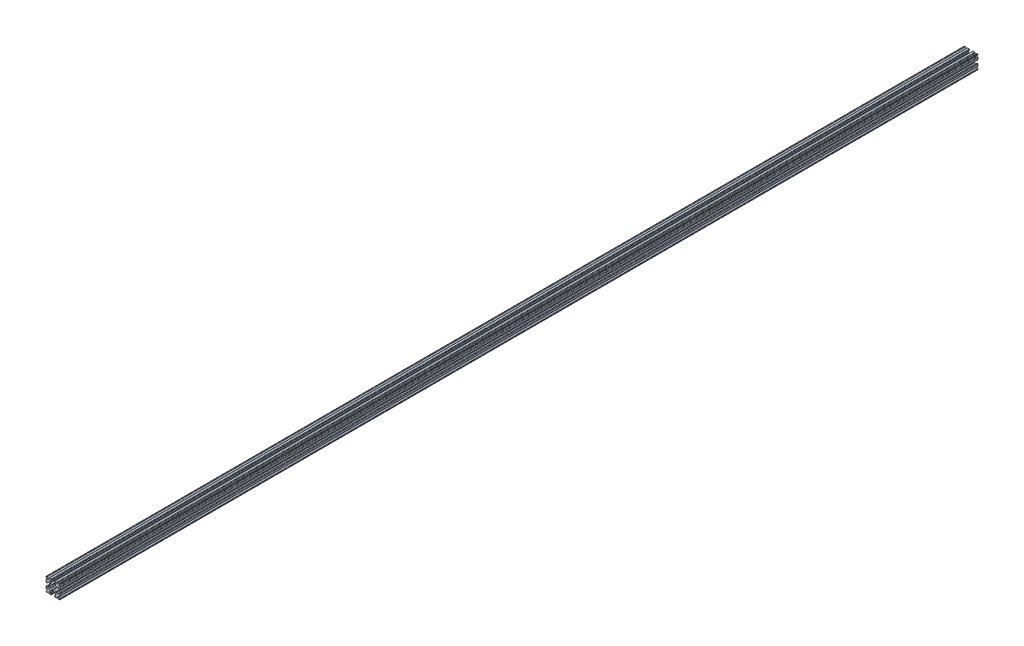
SolidWorks part; units mm, degrees
material "6063-T5"
ref_plane "Plano frontal" through (0, 0, 0) normal (0, 0, 1) x (1, 0, 0)
ref_plane "Plano superior" through (0, 0, 0) normal (0, 1, 0) x (1, 0, 0)
ref_plane "Plano direito" through (0, 0, 0) normal (1, 0, 0) x (0, 0, -1)
sketch "Model" plane through (0, 0, 0) normal (0, 0, 1) x (1, 0, 0)
  line L0 (53.34, -190.5) -> (99.06, -190.5)
  line L1 (111.76, -177.8) -> (111.76, -169.3613)
  line L2 (133.4403, -160.381) -> (159.8395, -186.7803)
  line L3 (168.8197, -190.5) -> (184.15, -190.5)
  line L4 (190.5, -184.15) -> (190.5, -168.8197)
  line L5 (186.7803, -159.8395) -> (160.381, -133.4403)
  line L6 (169.3613, -111.76) -> (177.8, -111.76)
  line L7 (190.5, -99.06) -> (190.5, -53.34)
  line L8 (177.8, -40.64) -> (167.64, -40.64)
  line L9 (154.94, -53.34) -> (154.94, -68.58)
  line L10 (149.86, -73.66) -> (96.5285, -73.66)
  line L11 (84.136, -63.7376) -> (80.2326, -46.3223)
  line L12 (80.2326, -46.3223) -> (33.4507, -19.3128)
  line L13 (33.4507, 19.3128) -> (80.2326, 46.3223)
  line L14 (80.2326, 46.3223) -> (84.136, 63.7376)
  line L15 (96.5285, 73.66) -> (149.86, 73.66)
  line L16 (154.94, 68.58) -> (154.94, 53.34)
  line L17 (167.64, 40.64) -> (177.8, 40.64)
  line L18 (190.5, 53.34) -> (190.5, 99.06)
  line L19 (177.8, 111.76) -> (169.3613, 111.76)
  line L20 (160.381, 133.4403) -> (186.7803, 159.8395)
  line L21 (190.5, 168.8197) -> (190.5, 184.15)
  line L22 (184.15, 190.5) -> (168.8197, 190.5)
  line L23 (159.8395, 186.7803) -> (133.4403, 160.381)
  line L24 (111.76, 169.3613) -> (111.76, 177.8)
  line L25 (99.06, 190.5) -> (53.34, 190.5)
  line L26 (40.64, 177.8) -> (40.64, 167.64)
  line L27 (53.34, 154.94) -> (68.58, 154.94)
  line L28 (73.66, 149.86) -> (73.66, 96.5285)
  line L29 (63.7376, 84.136) -> (24.9366, 75.4392)
  line L30 (20.9677, 70.4822) -> (20.9677, 64.6954)
  line L31 (15.8877, 59.6154) -> (-15.8877, 59.6154)
  line L32 (-20.9677, 64.6954) -> (-20.9677, 70.4822)
  line L33 (-24.9366, 75.4392) -> (-63.7376, 84.136)
  line L34 (-73.66, 96.5285) -> (-73.66, 149.86)
  line L35 (-68.58, 154.94) -> (-53.34, 154.94)
  line L36 (-40.64, 167.64) -> (-40.64, 177.8)
  line L37 (-53.34, 190.5) -> (-99.06, 190.5)
  line L38 (-111.76, 177.8) -> (-111.76, 169.3613)
  line L39 (-133.4403, 160.381) -> (-159.8395, 186.7803)
  line L40 (-168.8197, 190.5) -> (-184.15, 190.5)
  line L41 (-190.5, 184.15) -> (-190.5, 168.8197)
  line L42 (-186.7803, 159.8395) -> (-160.381, 133.4403)
  line L43 (-169.3613, 111.76) -> (-177.8, 111.76)
  line L44 (-190.5, 99.06) -> (-190.5, 53.34)
  line L45 (-177.8, 40.64) -> (-167.64, 40.64)
  line L46 (-154.94, 53.34) -> (-154.94, 68.58)
  line L47 (-149.86, 73.66) -> (-96.5285, 73.66)
  line L48 (-84.136, 63.7376) -> (-75.4392, 24.9366)
  line L49 (-70.4822, 20.9677) -> (-64.6954, 20.9677)
  line L50 (-59.6154, 15.8877) -> (-59.6154, -15.8877)
  line L51 (-64.6954, -20.9677) -> (-70.4822, -20.9677)
  line L52 (-75.4392, -24.9366) -> (-84.136, -63.7376)
  line L53 (-96.5285, -73.66) -> (-149.86, -73.66)
  line L54 (-154.94, -68.58) -> (-154.94, -53.34)
  line L55 (-167.64, -40.64) -> (-177.8, -40.64)
  line L56 (-190.5, -53.34) -> (-190.5, -99.06)
  line L57 (-177.8, -111.76) -> (-169.3613, -111.76)
  line L58 (-160.381, -133.4403) -> (-186.7803, -159.8395)
  line L59 (-190.5, -168.8197) -> (-190.5, -184.15)
  line L60 (-184.15, -190.5) -> (-168.8197, -190.5)
  line L61 (-159.8395, -186.7803) -> (-133.4403, -160.381)
  line L62 (-111.76, -169.3613) -> (-111.76, -177.8)
  line L63 (-99.06, -190.5) -> (-53.34, -190.5)
  line L64 (-40.64, -177.8) -> (-40.64, -167.64)
  line L65 (-53.34, -154.94) -> (-68.58, -154.94)
  line L66 (-73.66, -149.86) -> (-73.66, -96.5285)
  line L67 (-63.7376, -84.136) -> (-24.9366, -75.4392)
  line L68 (-20.9677, -70.4822) -> (-20.9677, -64.6954)
  line L69 (-15.8877, -59.6154) -> (15.8877, -59.6154)
  line L70 (20.9677, -64.6954) -> (20.9677, -70.4822)
  line L71 (24.9366, -75.4392) -> (63.7376, -84.136)
  line L72 (73.66, -96.5285) -> (73.66, -149.86)
  line L73 (68.58, -154.94) -> (53.34, -154.94)
  line L74 (40.64, -167.64) -> (40.64, -177.8)
  arc A0 (99.06, -190.5) -> (111.76, -177.8) centre (99.06, -177.8) ccw
  arc A1 (133.4403, -160.381) -> (111.76, -169.3613) centre (124.46, -169.3613) ccw
  arc A2 (159.8395, -186.7803) -> (168.8197, -190.5) centre (168.8197, -177.8) ccw
  arc A3 (184.15, -190.5) -> (190.5, -184.15) centre (184.15, -184.15) ccw
  arc A4 (190.5, -168.8197) -> (186.7803, -159.8395) centre (177.8, -168.8197) ccw
  arc A5 (169.3613, -111.76) -> (160.381, -133.4403) centre (169.3613, -124.46) ccw
  arc A6 (177.8, -111.76) -> (190.5, -99.06) centre (177.8, -99.06) ccw
  arc A7 (190.5, -53.34) -> (177.8, -40.64) centre (177.8, -53.34) ccw
  arc A8 (167.64, -40.64) -> (154.94, -53.34) centre (167.64, -53.34) ccw
  arc A9 (149.86, -73.66) -> (154.94, -68.58) centre (149.86, -68.58) ccw
  arc A10 (84.136, -63.7376) -> (96.5285, -73.66) centre (96.5285, -60.96) ccw
  arc A11 (33.4507, -19.3128) -> (23.9038, -20.8967) centre (29.6407, -25.9119) ccw
  arc A12 (23.9038, 20.8967) -> (23.9038, -20.8967) centre (0, 0) ccw
  arc A13 (23.9038, 20.8967) -> (33.4507, 19.3128) centre (29.6407, 25.9119) ccw
  arc A14 (96.5285, 73.66) -> (84.136, 63.7376) centre (96.5285, 60.96) ccw
  arc A15 (154.94, 68.58) -> (149.86, 73.66) centre (149.86, 68.58) ccw
  arc A16 (154.94, 53.34) -> (167.64, 40.64) centre (167.64, 53.34) ccw
  arc A17 (177.8, 40.64) -> (190.5, 53.34) centre (177.8, 53.34) ccw
  arc A18 (190.5, 99.06) -> (177.8, 111.76) centre (177.8, 99.06) ccw
  arc A19 (160.381, 133.4403) -> (169.3613, 111.76) centre (169.3613, 124.46) ccw
  arc A20 (186.7803, 159.8395) -> (190.5, 168.8197) centre (177.8, 168.8197) ccw
  arc A21 (190.5, 184.15) -> (184.15, 190.5) centre (184.15, 184.15) ccw
  arc A22 (168.8197, 190.5) -> (159.8395, 186.7803) centre (168.8197, 177.8) ccw
  arc A23 (111.76, 169.3613) -> (133.4403, 160.381) centre (124.46, 169.3613) ccw
  arc A24 (111.76, 177.8) -> (99.06, 190.5) centre (99.06, 177.8) ccw
  arc A25 (53.34, 190.5) -> (40.64, 177.8) centre (53.34, 177.8) ccw
  arc A26 (40.64, 167.64) -> (53.34, 154.94) centre (53.34, 167.64) ccw
  arc A27 (73.66, 149.86) -> (68.58, 154.94) centre (68.58, 149.86) ccw
  arc A28 (63.7376, 84.136) -> (73.66, 96.5285) centre (60.96, 96.5285) ccw
  arc A29 (24.9366, 75.4392) -> (20.9677, 70.4822) centre (26.0477, 70.4822) ccw
  arc A30 (15.8877, 59.6154) -> (20.9677, 64.6954) centre (15.8877, 64.6954) ccw
  arc A31 (-20.9677, 64.6954) -> (-15.8877, 59.6154) centre (-15.8877, 64.6954) ccw
  arc A32 (-20.9677, 70.4822) -> (-24.9366, 75.4392) centre (-26.0477, 70.4822) ccw
  arc A33 (-73.66, 96.5285) -> (-63.7376, 84.136) centre (-60.96, 96.5285) ccw
  arc A34 (-68.58, 154.94) -> (-73.66, 149.86) centre (-68.58, 149.86) ccw
  arc A35 (-53.34, 154.94) -> (-40.64, 167.64) centre (-53.34, 167.64) ccw
  arc A36 (-40.64, 177.8) -> (-53.34, 190.5) centre (-53.34, 177.8) ccw
  arc A37 (-99.06, 190.5) -> (-111.76, 177.8) centre (-99.06, 177.8) ccw
  arc A38 (-133.4403, 160.381) -> (-111.76, 169.3613) centre (-124.46, 169.3613) ccw
  arc A39 (-159.8395, 186.7803) -> (-168.8197, 190.5) centre (-168.8197, 177.8) ccw
  arc A40 (-184.15, 190.5) -> (-190.5, 184.15) centre (-184.15, 184.15) ccw
  arc A41 (-190.5, 168.8197) -> (-186.7803, 159.8395) centre (-177.8, 168.8197) ccw
  arc A42 (-169.3613, 111.76) -> (-160.381, 133.4403) centre (-169.3613, 124.46) ccw
  arc A43 (-177.8, 111.76) -> (-190.5, 99.06) centre (-177.8, 99.06) ccw
  arc A44 (-190.5, 53.34) -> (-177.8, 40.64) centre (-177.8, 53.34) ccw
  arc A45 (-167.64, 40.64) -> (-154.94, 53.34) centre (-167.64, 53.34) ccw
  arc A46 (-149.86, 73.66) -> (-154.94, 68.58) centre (-149.86, 68.58) ccw
  arc A47 (-84.136, 63.7376) -> (-96.5285, 73.66) centre (-96.5285, 60.96) ccw
  arc A48 (-75.4392, 24.9366) -> (-70.4822, 20.9677) centre (-70.4822, 26.0477) ccw
  arc A49 (-59.6154, 15.8877) -> (-64.6954, 20.9677) centre (-64.6954, 15.8877) ccw
  arc A50 (-64.6954, -20.9677) -> (-59.6154, -15.8877) centre (-64.6954, -15.8877) ccw
  arc A51 (-70.4822, -20.9677) -> (-75.4392, -24.9366) centre (-70.4822, -26.0477) ccw
  arc A52 (-96.5285, -73.66) -> (-84.136, -63.7376) centre (-96.5285, -60.96) ccw
  arc A53 (-154.94, -68.58) -> (-149.86, -73.66) centre (-149.86, -68.58) ccw
  arc A54 (-154.94, -53.34) -> (-167.64, -40.64) centre (-167.64, -53.34) ccw
  arc A55 (-177.8, -40.64) -> (-190.5, -53.34) centre (-177.8, -53.34) ccw
  arc A56 (-190.5, -99.06) -> (-177.8, -111.76) centre (-177.8, -99.06) ccw
  arc A57 (-160.381, -133.4403) -> (-169.3613, -111.76) centre (-169.3613, -124.46) ccw
  arc A58 (-186.7803, -159.8395) -> (-190.5, -168.8197) centre (-177.8, -168.8197) ccw
  arc A59 (-190.5, -184.15) -> (-184.15, -190.5) centre (-184.15, -184.15) ccw
  arc A60 (-168.8197, -190.5) -> (-159.8395, -186.7803) centre (-168.8197, -177.8) ccw
  arc A61 (-111.76, -169.3613) -> (-133.4403, -160.381) centre (-124.46, -169.3613) ccw
  arc A62 (-111.76, -177.8) -> (-99.06, -190.5) centre (-99.06, -177.8) ccw
  arc A63 (-53.34, -190.5) -> (-40.64, -177.8) centre (-53.34, -177.8) ccw
  arc A64 (-40.64, -167.64) -> (-53.34, -154.94) centre (-53.34, -167.64) ccw
  arc A65 (-73.66, -149.86) -> (-68.58, -154.94) centre (-68.58, -149.86) ccw
  arc A66 (-63.7376, -84.136) -> (-73.66, -96.5285) centre (-60.96, -96.5285) ccw
  arc A67 (-24.9366, -75.4392) -> (-20.9677, -70.4822) centre (-26.0477, -70.4822) ccw
  arc A68 (-15.8877, -59.6154) -> (-20.9677, -64.6954) centre (-15.8877, -64.6954) ccw
  arc A69 (20.9677, -64.6954) -> (15.8877, -59.6154) centre (15.8877, -64.6954) ccw
  arc A70 (20.9677, -70.4822) -> (24.9366, -75.4392) centre (26.0477, -70.4822) ccw
  arc A71 (73.66, -96.5285) -> (63.7376, -84.136) centre (60.96, -96.5285) ccw
  arc A72 (68.58, -154.94) -> (73.66, -149.86) centre (68.58, -149.86) ccw
  arc A73 (53.34, -154.94) -> (40.64, -167.64) centre (53.34, -167.64) ccw
  arc A74 (40.64, -177.8) -> (53.34, -190.5) centre (53.34, -177.8) ccw
extrude "Ressalto-extrusão1" add sketch "Model" along normal blind 25400
scale "Escala2" scale about origin uniform scaling yes scale factor 0.03937
